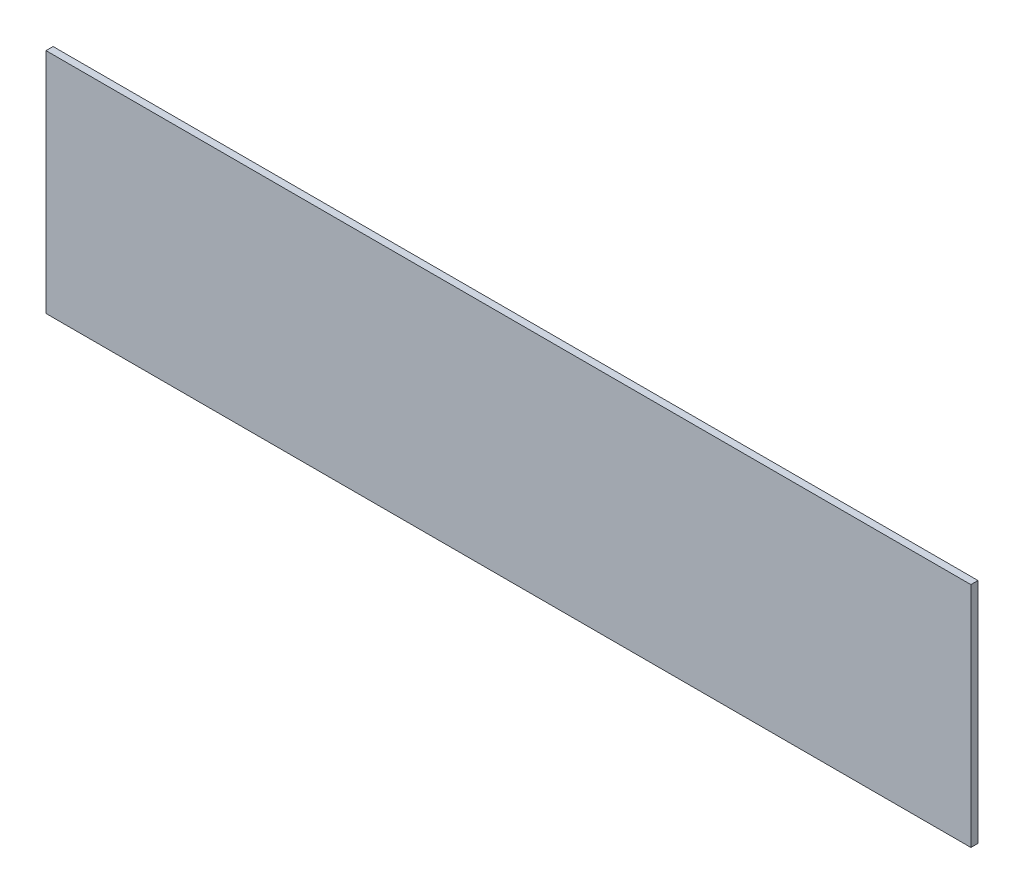
SolidWorks part; units mm, degrees
ref_plane "Alzado" through (0, 0, 0) normal (0, 0, 1) x (1, 0, 0)
ref_plane "Planta" through (0, 0, 0) normal (0, 1, 0) x (1, 0, 0)
ref_plane "Vista lateral" through (0, 0, 0) normal (1, 0, 0) x (0, 0, -1)
sketch "Croquis1" plane through (0, 0, 0) normal (0, 0, 1) x (1, 0, 0)
  line L1 (-130, 32) -> (130, 32)
  line L2 (-130, 32) -> (-130, -32)
  line L3 (-130, -32) -> (130, -32)
  line L4 (130, 32) -> (130, -32)
  line L5 (-130, 32) -> (130, -32) construction
  line L6 (-130, -32) -> (130, 32) construction
  point P0 (0, 0)
  dimension "D1" = 260
  dimension "D2" = 64
extrude "Saliente-Extruir1" add sketch "Croquis1" along normal blind 2
